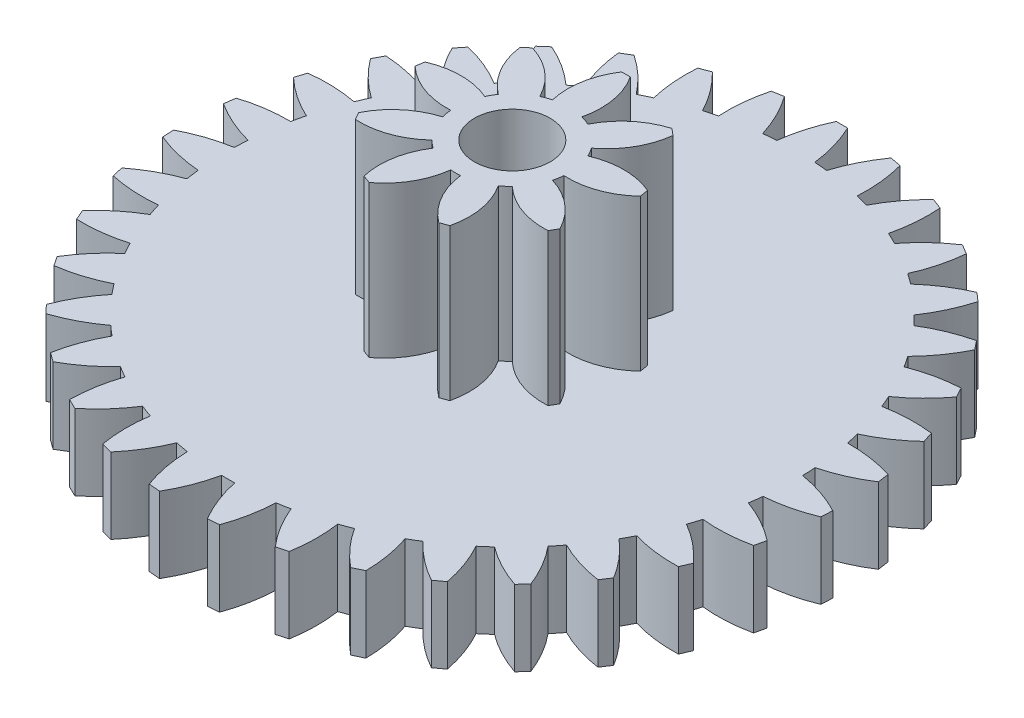
SolidWorks part; units mm, degrees
material "PBT General Purpose"
ref_plane "Front Plane" through (0, 0, 0) normal (0, 0, 1) x (1, 0, 0)
ref_plane "Top Plane" through (0, 0, 0) normal (0, 1, 0) x (1, 0, 0)
ref_plane "Right Plane" through (0, 0, 0) normal (1, 0, 0) x (0, 0, -1)
sketch "Sketch1" plane through (0, 0, 0) normal (0, 1, 0) x (1, 0, 0)
  circle A0 centre (0, 0) radius 7.5
  dimension "D1" = 15
extrude "Boss-Extrude1" add sketch "Sketch1" along normal blind 2
sketch "Sketch2" plane through (0, 2, 0) normal (0, 1, 0) x (1, 0, 0)
  line L0 (0, 0) -> (0, 8) construction
  line L1 (0, 0) -> (0.5, 7.4833) construction
  line L2 (0, 0) -> (-0.5, 7.4833) construction
  line L3 (-0.15, 8.7) -> (0.15, 8.7)
  line L4 (-0.5, 7.4833) -> (0.5, 7.4833) construction
  arc A0 (-0.5, 7.4833) -> (-0.15, 8.7) centre (3.4707, 6.9998) cw
  arc A1 (0.5, 7.4833) -> (0.15, 8.7) centre (-3.4707, 6.9998) ccw
  arc A2 (-0.5, 7.4833) -> (0.5, 7.4833) centre (0, 0) cw
  circle A3 centre (0, 0) radius 7.5 construction
  point P7 (0, 7.4833)
  point P10 (0, 8.7)
  dimension "D3" = 0.3
  dimension "D6" = 4
  dimension "D2" = 8
  dimension "D4" = 1
  dimension "D5" = 8.7
extrude "Boss-Extrude2" add sketch "Sketch2" against normal up to surface (2 mm away) up to face at (0, 0, 7.5)
pattern_circular "CirPattern1" count 35 over 360 about axis through (0, 0, 0) along (0, 1, 0) of "Boss-Extrude2"
sketch "Sketch3" plane through (0, 2, 0) normal (0, 1, 0) x (1, 0, 0)
  circle A0 centre (0, 0) radius 1.5
  dimension "D1" = 3
extrude "Boss-Extrude3" add sketch "Sketch3" along normal blind 4
sketch "Sketch4" plane through (0, 6, 0) normal (0, 1, 0) x (1, 0, 0)
  line L0 (0, 0) -> (0, 3) construction
  line L1 (-0.115, 3) -> (0.115, 3)
  line L2 (0, 0) -> (0.3882, 1.4489) construction
  line L3 (0, 0) -> (-0.3882, 1.4489) construction
  arc A1 (-0.115, 3) -> (-0.3882, 1.4489) centre (1.5589, 1.9055) ccw
  circle A2 centre (0, 0) radius 1.5 construction
  arc A3 (0.115, 3) -> (0.3882, 1.4489) centre (-1.5589, 1.9055) cw
  circle A5 centre (0, 0) radius 1.5
  arc A6 (0.3882, 1.4489) -> (-0.3882, 1.4489) centre (0, 0) ccw
  point P6 (0, 3)
  dimension "D2" = 15
  dimension "D3" = 2
  dimension "D1" = 3
  dimension "D4" = 0.23
  dimension "D5" = 0
extrude "Boss-Extrude4" add sketch "Sketch4" against normal up to surface (4 mm away) up to face at (0, 2, 1.5)
pattern_circular "CirPattern2" count 9 over 360 about axis through (0, 0, 0) along (0, 1, 0) of "Boss-Extrude4"
sketch "Sketch5" plane through (0, 6, 0) normal (0, 1, 0) x (1, 0, 0)
  circle A0 centre (0, 0) radius 1
  dimension "D1" = 2
extrude "Cut-Extrude1" cut sketch "Sketch5" against normal through all both and the other way through all
sketch "Sketch6" plane through (0, 0, 0) normal (0, -1, 0) x (1, 0, 0)
  circle A0 centre (0, 0) radius 1 construction
  circle A1 centre (0, 0) radius 1
  circle A2 centre (0, 0) radius 1.5
  dimension "D1" = 0.5
extrude "Boss-Extrude5" add sketch "Sketch6" along normal blind 0.4
